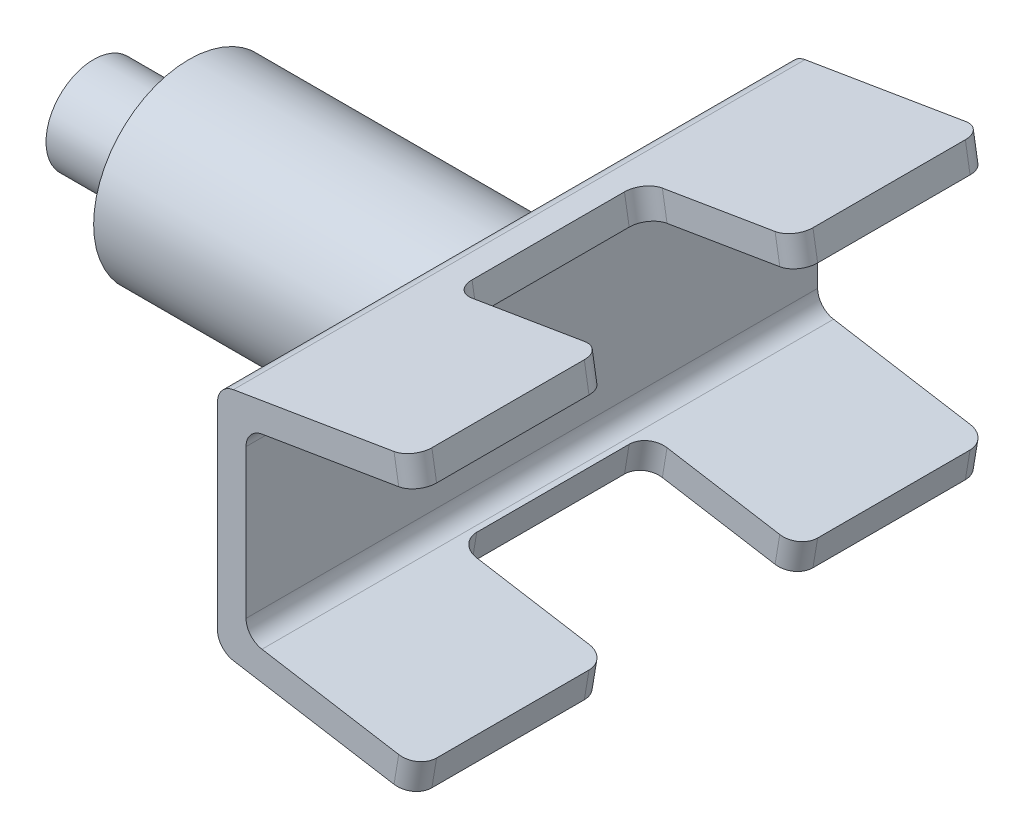
SolidWorks part; units mm, degrees
ref_plane "Front Plane" through (0, 0, 0) normal (0, 0, 1) x (1, 0, 0)
ref_plane "Top Plane" through (0, 0, 0) normal (0, 1, 0) x (1, 0, 0)
ref_plane "Right Plane" through (0, 0, 0) normal (1, 0, 0) x (0, 0, -1)
sketch "Sketch1" plane through (0, 0, 0) normal (1, 0, 0) x (0, 0, -1)
  circle A0 centre (0, 0) radius 127
  dimension "D1" = 254
extrude "Boss-Extrude1" add sketch "Sketch1" along normal mid plane 127
sketch "Sketch2" plane through (0, 0, 0) normal (0, 0, 1) x (1, 0, 0)
  line L11 (88.9, -120.65) -> (88.9, 120.65)
  line L15 (-63.5, 127) -> (-63.5, -127) construction
  line L16 (311.2364, 196.3316) -> (50.8, 152.9255)
  line L20 (317.5, 158.75) -> (88.9, 120.65)
  line L21 (88.9, -120.65) -> (317.5, -158.75)
  line L22 (50.8, -152.9255) -> (50.8, 152.9255)
  line L23 (50.8, -152.9255) -> (311.2364, -196.3316)
  line L24 (311.2364, -196.3316) -> (317.5, -158.75)
  line L25 (317.5, 158.75) -> (311.2364, 196.3316)
  point P3 (63.5, -177.8)
  point P7 (88.9, 0)
  point P13 (317.5, 0)
  point P14 (63.5, 177.8)
  dimension "D1" = 241.3
  dimension "D2" = 99.462
  dimension "D3" = 99.462
  dimension "D4" = 152.4
  dimension "D5" = 0
  dimension "D6" = 38.1
extrude "Boss-Extrude2" add sketch "Sketch2" along normal mid plane 762
sketch "Sketch3" plane through (334.6622, 55.777, 0) normal (0.9864, 0.1644, 0) x (0, 0, -1)
  line L0 (0, 104.3934) -> (-127, 104.3934)
  line L1 (-381, 104.3934) -> (381, 104.3934) construction
  line L2 (-381, 104.3934) -> (381, 104.3934) construction
  line L3 (0, 104.3934) -> (127, 104.3934)
  line L4 (127, 104.3934) -> (127, 142.4934)
  line L5 (-381, 142.4934) -> (381, 142.4934) construction
  line L6 (127, 142.4934) -> (-127, 142.4934)
  line L7 (-127, 142.4934) -> (-127, 104.3934)
  dimension "D1" = 127
  dimension "D2" = 127
extrude "Cut-Extrude1" cut sketch "Sketch3" against normal blind 203.2
sketch "Sketch4" plane through (334.6622, -55.777, 0) normal (0.9864, -0.1644, 0) x (0, 0, -1)
  line L0 (0, -142.4934) -> (-127, -142.4934)
  line L1 (-381, -142.4934) -> (381, -142.4934) construction
  line L2 (0, -142.4934) -> (127, -142.4934)
  line L3 (127, -142.4934) -> (127, -104.3934)
  line L4 (-381, -104.3934) -> (381, -104.3934) construction
  line L5 (127, -104.3934) -> (-127, -104.3934)
  line L6 (-381, -104.3934) -> (381, -104.3934) construction
  line L7 (-127, -104.3934) -> (-127, -142.4934)
  dimension "D1" = 127
  dimension "D2" = 127
extrude "Cut-Extrude2" cut sketch "Sketch4" against normal blind 203.2
fillet "Fillet1" radius 25.4 2 edges at (88.9, 120.65, 0) (88.9, -120.65, 0)
fillet "Fillet2" radius 25.4 2 edges at (50.8, -152.9255, 0) (50.8, 152.9255, 0)
fillet "Fillet3" radius 25.4 12 edges at (314.3682, -177.5408, -381) (314.3682, -177.5408, -127) (314.3682, -177.5408, 381) (314.3682, -177.5408, 127) (113.933, -144.1349, -127) (113.933, -144.1349, 127) (314.3682, 177.5408, -381) (314.3682, 177.5408, 381) (314.3682, 177.5408, -127) (314.3682, 177.5408, 127) (113.933, 144.1349, -127) (113.933, 144.1349, 127)
sketch "Sketch5" plane through (-63.5, 0, 0) normal (-1, 0, 0) x (0, 0, 1)
  circle A1 centre (0, 0) radius 127
  circle A2 centre (0, 0) radius 127
  dimension "D1" = 0
extrude "Boss-Extrude3" add sketch "Sketch5" along normal blind 304.8
sketch "Sketch6" plane through (-368.3, 0, 0) normal (-1, 0, 0) x (0, 0, 1)
  circle A0 centre (0, 0) radius 63.5
  dimension "D1" = 127
extrude "Boss-Extrude4" add sketch "Sketch6" along normal blind 127
